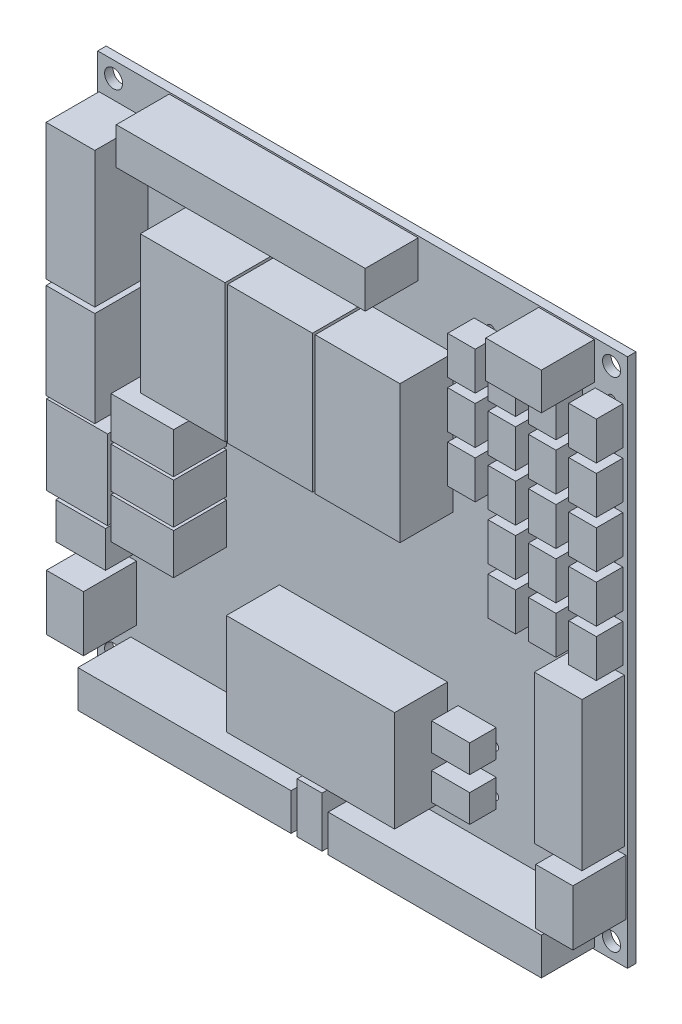
SolidWorks part; units mm, degrees
ref_plane "Face" through (0, 0, 0) normal (0, 0, 1) x (1, 0, 0)
ref_plane "Dessus" through (0, 0, 0) normal (0, 1, 0) x (1, 0, 0)
ref_plane "Droite" through (0, 0, 0) normal (1, 0, 0) x (0, 0, -1)
sketch "Esquisse1" plane through (0, 0, 0) normal (0, 0, 1) x (1, 0, 0)
  line B0 (0.0508, 0.0508) -> (100.0508, 0.0508)
  line B1 (100.0508, 0.0508) -> (100.0508, 100.0508)
  line B2 (100.0508, 100.0508) -> (0.0508, 100.0508)
  line B3 (0.0508, 100.0508) -> (0.0508, 0.0508)
  circle B4 centre (3.0508, 97.0508) radius 1.7
  circle B5 centre (97.0508, 97.0508) radius 1.7
  circle B6 centre (97.0508, 3.0508) radius 1.7
  circle B7 centre (3.0508, 3.0508) radius 1.7
  circle B8 centre (7.4058, 64.0408) radius 1.2
  circle B9 centre (7.4058, 51.6308) radius 1.2
  circle B10 centre (74.9838, 23.9048) radius 0.75
  circle B11 centre (74.9838, 15.7768) radius 0.75
  circle B12 centre (81.8608, 91.6208) radius 0.75
  circle B13 centre (81.8608, 82.7308) radius 0.75
  circle B14 centre (81.8608, 73.8408) radius 0.75
  circle B15 centre (81.8608, 64.9508) radius 0.75
  circle B16 centre (81.8608, 56.0608) radius 0.75
  circle B17 centre (74.2408, 91.6208) radius 0.75
  circle B18 centre (74.2408, 82.7308) radius 0.75
  circle B19 centre (74.2408, 73.8408) radius 0.75
  circle B20 centre (97.1008, 91.6208) radius 0.75
  circle B21 centre (97.1008, 82.7308) radius 0.75
  circle B22 centre (97.1008, 73.8408) radius 0.75
  circle B23 centre (97.1008, 64.9508) radius 0.75
  circle B24 centre (97.1008, 56.0608) radius 0.75
  circle B25 centre (89.4808, 91.6208) radius 0.75
  circle B26 centre (89.4808, 82.7308) radius 0.75
  circle B27 centre (89.4808, 73.8408) radius 0.75
  circle B28 centre (89.4808, 64.9508) radius 0.75
  circle B29 centre (89.4808, 56.0608) radius 0.75
  circle B30 centre (7.4058, 90.7108) radius 1.2
  circle B31 centre (7.4058, 70.6808) radius 1.2
  circle B32 centre (6.0528, 29.0658) radius 0.45
  circle B33 centre (6.0528, 24.6658) radius 0.45
sketch_block_instance "BlueBoard_v1-1"
sketch_block "BlueBoard_v1"
extrude "Boss.-Extru.1" add sketch "Esquisse1" along normal blind 1.6
sketch "Esquisse2" plane through (0, 0, 0) normal (0, 0, 1) x (1, 0, 0)
  circle A0 centre (97.0508, 97.0508) radius 1.7 construction
  circle A1 centre (97.0508, 3.0508) radius 1.7 construction
sketch_block_instance "BlueBoard_v1_top-1"
sketch_block "BlueBoard_v1_top"
sketch "Esquisse3" plane through (0, 0, 1.6) normal (0, 0, 1) x (1, 0, 0)
  line L1 (0.3058, 67.8858) -> (9.5058, 67.8858)
  line L2 (0.3058, 67.8858) -> (0.3058, 93.5058)
  line L3 (0.3058, 93.5058) -> (9.5058, 93.5058)
  line L4 (9.5058, 67.8858) -> (9.5058, 93.5058)
  line L5 (0.3058, 66.8358) -> (9.5058, 66.8358)
  line L6 (0.3058, 66.8358) -> (0.3058, 48.8358)
  line L7 (0.3058, 48.8358) -> (9.5058, 48.8358)
  line L8 (9.5058, 66.8358) -> (9.5058, 48.8358)
  line L9 (0.4058, 48.3508) -> (11.9058, 48.3508)
  line L10 (0.4058, 48.3508) -> (0.4058, 33.3508)
  line L11 (0.4058, 33.3508) -> (11.9058, 33.3508)
  line L12 (11.9058, 48.3508) -> (11.9058, 33.3508)
  line L13 (18.0858, 58.1708) -> (34.0858, 58.1708)
  line L14 (18.0858, 58.1708) -> (18.0858, 84.1708)
  line L15 (18.0858, 84.1708) -> (34.0858, 84.1708)
  line L16 (34.0858, 58.1708) -> (34.0858, 84.1708)
  line L17 (34.5958, 84.1708) -> (50.5958, 84.1708)
  line L18 (34.5958, 84.1708) -> (34.5958, 58.1708)
  line L19 (34.5958, 58.1708) -> (50.5958, 58.1708)
  line L20 (50.5958, 84.1708) -> (50.5958, 58.1708)
  line L21 (51.1058, 58.1708) -> (67.1058, 58.1708)
  line L22 (51.1058, 58.1708) -> (51.1058, 84.1708)
  line L23 (51.1058, 84.1708) -> (67.1058, 84.1708)
  line L24 (67.1058, 58.1708) -> (67.1058, 84.1708)
  line L25 (34.3408, 10.8458) -> (66.0908, 10.8458)
  line L26 (34.3408, 10.8458) -> (34.3408, 29.8958)
  line L27 (34.3408, 29.8958) -> (66.0908, 29.8958)
  line L28 (66.0908, 10.8458) -> (66.0908, 29.8958)
  line L29 (12.5658, 55.2808) -> (24.3658, 55.2808)
  line L30 (12.5658, 55.2808) -> (12.5658, 47.5808)
  line L31 (12.5658, 47.5808) -> (24.3658, 47.5808)
  line L32 (24.3658, 55.2808) -> (24.3658, 47.5808)
  line L33 (24.3658, 47.0258) -> (12.5658, 47.0258)
  line L34 (24.3658, 47.0258) -> (24.3658, 39.3258)
  line L35 (24.3658, 39.3258) -> (12.5658, 39.3258)
  line L36 (12.5658, 47.0258) -> (12.5658, 39.3258)
  line L37 (12.5658, 38.7708) -> (24.3658, 38.7708)
  line L38 (12.5658, 38.7708) -> (12.5658, 31.0708)
  line L39 (12.5658, 31.0708) -> (24.3658, 31.0708)
  line L40 (24.3658, 38.7708) -> (24.3658, 31.0708)
extrude "Boss.-Extru.2" add sketch "Esquisse3" along normal blind 10
sketch "Esquisse4" plane through (0, 0, 1.6) normal (0, 0, 1) x (1, 0, 0)
  line L1 (13.5508, 92.7408) -> (60.5508, 92.7408)
  line L2 (13.5508, 92.7408) -> (13.5508, 99.7408)
  line L3 (13.5508, 99.7408) -> (60.5508, 99.7408)
  line L4 (60.5508, 92.7408) -> (60.5508, 99.7408)
  line L5 (83.3008, 99.7408) -> (93.8008, 99.7408)
  line L6 (83.3008, 99.7408) -> (83.3008, 92.7408)
  line L7 (83.3008, 92.7408) -> (93.8008, 92.7408)
  line L8 (93.8008, 99.7408) -> (93.8008, 92.7408)
  line L9 (6.3008, 7.3608) -> (46.5508, 7.3608)
  line L10 (6.3008, 7.3608) -> (6.3008, 0.3608)
  line L11 (6.3008, 0.3608) -> (46.5508, 0.3608)
  line L12 (46.5508, 7.3608) -> (46.5508, 0.3608)
  line L13 (53.5508, 7.3608) -> (93.8008, 7.3608)
  line L14 (53.5508, 7.3608) -> (53.5508, 0.3608)
  line L15 (53.5508, 0.3608) -> (93.8008, 0.3608)
  line L16 (93.8008, 7.3608) -> (93.8008, 0.3608)
  line L17 (92.7408, 18.3958) -> (99.7408, 18.3958)
  line L18 (92.7408, 18.3958) -> (92.7408, 7.8958)
  line L19 (92.7408, 7.8958) -> (99.7408, 7.8958)
  line L20 (99.7408, 18.3958) -> (99.7408, 7.8958)
  line L21 (0.3608, 9.8008) -> (7.3608, 9.8008)
  line L22 (0.3608, 9.8008) -> (0.3608, 20.3008)
  line L23 (0.3608, 20.3008) -> (7.3608, 20.3008)
  line L24 (7.3608, 9.8008) -> (7.3608, 20.3008)
  line L25 (47.7008, 9.8808) -> (52.4008, 9.8808)
  line L26 (47.7008, 9.8808) -> (47.7008, 0.3808)
  line L27 (47.7008, 0.3808) -> (52.4008, 0.3808)
  line L28 (52.4008, 9.8808) -> (52.4008, 0.3808)
extrude "Boss.-Extru.3" add sketch "Esquisse4" along normal blind 10
sketch "Esquisse5" plane through (0, 0, 1.6) normal (0, 0, 1) x (1, 0, 0)
  line L1 (71.1108, 91.9158) -> (76.3108, 91.9158)
  line L2 (71.1108, 91.9158) -> (71.1108, 84.7158)
  line L3 (71.1108, 84.7158) -> (76.3108, 84.7158)
  line L4 (76.3108, 91.9158) -> (76.3108, 84.7158)
  line L5 (78.7308, 84.7158) -> (83.9308, 84.7158)
  line L6 (78.7308, 84.7158) -> (78.7308, 91.9158)
  line L7 (78.7308, 91.9158) -> (83.9308, 91.9158)
  line L8 (83.9308, 84.7158) -> (83.9308, 91.9158)
  line L9 (86.3508, 91.9158) -> (91.5508, 91.9158)
  line L10 (86.3508, 91.9158) -> (86.3508, 84.7158)
  line L11 (86.3508, 84.7158) -> (91.5508, 84.7158)
  line L12 (91.5508, 91.9158) -> (91.5508, 84.7158)
  line L13 (93.9708, 91.9158) -> (99.1708, 91.9158)
  line L14 (93.9708, 91.9158) -> (93.9708, 84.7158)
  line L15 (93.9708, 84.7158) -> (99.1708, 84.7158)
  line L16 (99.1708, 91.9158) -> (99.1708, 84.7158)
  line L17 (99.1708, 83.0258) -> (93.9708, 83.0258)
  line L18 (99.1708, 83.0258) -> (99.1708, 75.8258)
  line L19 (99.1708, 75.8258) -> (93.9708, 75.8258)
  line L20 (93.9708, 83.0258) -> (93.9708, 75.8258)
  line L21 (91.5508, 75.8258) -> (86.3508, 75.8258)
  line L22 (91.5508, 75.8258) -> (91.5508, 83.0258)
  line L23 (91.5508, 83.0258) -> (86.3508, 83.0258)
  line L24 (86.3508, 75.8258) -> (86.3508, 83.0258)
  line L25 (83.9308, 83.0258) -> (78.7308, 83.0258)
  line L26 (83.9308, 83.0258) -> (83.9308, 75.8258)
  line L27 (83.9308, 75.8258) -> (78.7308, 75.8258)
  line L28 (78.7308, 83.0258) -> (78.7308, 75.8258)
  line L29 (76.3108, 75.8258) -> (71.1108, 75.8258)
  line L30 (76.3108, 75.8258) -> (76.3108, 83.0258)
  line L31 (76.3108, 83.0258) -> (71.1108, 83.0258)
  line L32 (71.1108, 75.8258) -> (71.1108, 83.0258)
  line L33 (71.1108, 66.9358) -> (76.3108, 66.9358)
  line L34 (71.1108, 66.9358) -> (71.1108, 74.1358)
  line L35 (71.1108, 74.1358) -> (76.3108, 74.1358)
  line L36 (76.3108, 66.9358) -> (76.3108, 74.1358)
  line L37 (78.7308, 74.1358) -> (83.9308, 74.1358)
  line L38 (78.7308, 74.1358) -> (78.7308, 66.9358)
  line L39 (78.7308, 66.9358) -> (83.9308, 66.9358)
  line L40 (83.9308, 74.1358) -> (83.9308, 66.9358)
  line L41 (86.3508, 66.9358) -> (91.5508, 66.9358)
  line L42 (86.3508, 66.9358) -> (86.3508, 74.1358)
  line L43 (86.3508, 74.1358) -> (91.5508, 74.1358)
  line L44 (91.5508, 66.9358) -> (91.5508, 74.1358)
  line L45 (93.9708, 74.1358) -> (99.1708, 74.1358)
  line L46 (93.9708, 74.1358) -> (93.9708, 66.9358)
  line L47 (93.9708, 66.9358) -> (99.1708, 66.9358)
  line L48 (99.1708, 74.1358) -> (99.1708, 66.9358)
  line L49 (99.1708, 65.2458) -> (93.9708, 65.2458)
  line L50 (99.1708, 65.2458) -> (99.1708, 58.0458)
  line L51 (99.1708, 58.0458) -> (93.9708, 58.0458)
  line L52 (93.9708, 65.2458) -> (93.9708, 58.0458)
  line L53 (91.5508, 58.0458) -> (86.3508, 58.0458)
  line L54 (91.5508, 58.0458) -> (91.5508, 65.2458)
  line L55 (91.5508, 65.2458) -> (86.3508, 65.2458)
  line L56 (86.3508, 58.0458) -> (86.3508, 65.2458)
  line L57 (83.9308, 65.2458) -> (78.7308, 65.2458)
  line L58 (83.9308, 65.2458) -> (83.9308, 58.0458)
  line L59 (83.9308, 58.0458) -> (78.7308, 58.0458)
  line L60 (78.7308, 65.2458) -> (78.7308, 58.0458)
  line L61 (78.7308, 56.3558) -> (83.9308, 56.3558)
  line L62 (78.7308, 56.3558) -> (78.7308, 49.1558)
  line L63 (78.7308, 49.1558) -> (83.9308, 49.1558)
  line L64 (83.9308, 56.3558) -> (83.9308, 49.1558)
  line L65 (86.3508, 49.1558) -> (91.5508, 49.1558)
  line L66 (86.3508, 49.1558) -> (86.3508, 56.3558)
  line L67 (86.3508, 56.3558) -> (91.5508, 56.3558)
  line L68 (91.5508, 49.1558) -> (91.5508, 56.3558)
  line L69 (93.9708, 56.3558) -> (99.1708, 56.3558)
  line L70 (93.9708, 56.3558) -> (93.9708, 49.1558)
  line L71 (93.9708, 49.1558) -> (99.1708, 49.1558)
  line L72 (99.1708, 56.3558) -> (99.1708, 49.1558)
  line L73 (68.0788, 13.7068) -> (75.2788, 13.7068)
  line L74 (68.0788, 13.7068) -> (68.0788, 18.9068)
  line L75 (68.0788, 18.9068) -> (75.2788, 18.9068)
  line L76 (75.2788, 13.7068) -> (75.2788, 18.9068)
  line L77 (68.0788, 21.8348) -> (75.2788, 21.8348)
  line L78 (68.0788, 21.8348) -> (68.0788, 27.0348)
  line L79 (68.0788, 27.0348) -> (75.2788, 27.0348)
  line L80 (75.2788, 21.8348) -> (75.2788, 27.0348)
extrude "Boss.-Extru.4" add sketch "Esquisse5" along normal blind 5
sketch "Esquisse6" plane through (0, 0, 1.6) normal (0, 0, 1) x (1, 0, 0)
  line L1 (0.1346, 30.7074) -> (9.5309, 30.7074)
  line L2 (0.1346, 30.7074) -> (0.1346, 23.8549)
  line L3 (0.1346, 23.8549) -> (9.5309, 23.8549)
  line L4 (9.5309, 30.7074) -> (9.5309, 23.8549)
  line L5 (90.4658, 47.7058) -> (99.4658, 47.7058)
  line L6 (90.4658, 47.7058) -> (90.4658, 19.7058)
  line L7 (90.4658, 19.7058) -> (99.4658, 19.7058)
  line L8 (99.4658, 47.7058) -> (99.4658, 19.7058)
extrude "Boss.-Extru.5" add sketch "Esquisse6" along normal blind 8
